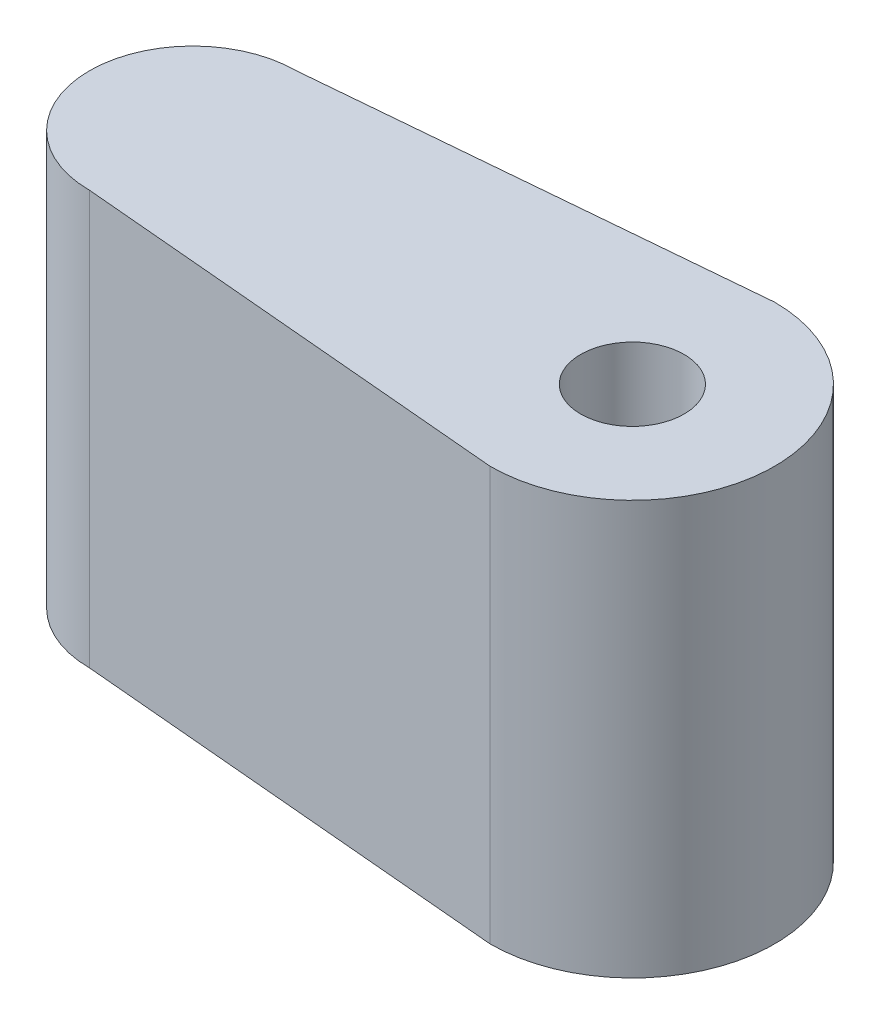
SolidWorks part; units mm, degrees
ref_plane "Front Plane" through (0, 0, 0) normal (0, 0, 1) x (1, 0, 0)
ref_plane "Top Plane" through (0, 0, 0) normal (0, 1, 0) x (1, 0, 0)
ref_plane "Right Plane" through (0, 0, 0) normal (1, 0, 0) x (0, 0, -1)
sketch "Sketch1" plane through (0, 0, 0) normal (0, 1, 0) x (1, 0, 0)
  line L0 (0, 0) -> (-8.5, 0) construction
  line L1 (-8.5, 2) -> (0, 2.75)
  line L2 (-8.5, -2) -> (0, -2.75)
  circle A0 centre (0, 0) radius 1
  arc A1 (-0.4815, -2.7075) -> (-0.4815, 2.7075) centre (0, 0) ccw
  arc A2 (-8.5, 2) -> (-8.5, -2) centre (-8.5, 0) ccw
  dimension "D1" = 2
  dimension "D2" = 5.5
  dimension "D3" = 4
  dimension "D4" = 8.5
extrude "Boss-Extrude1" add sketch "Sketch1" along normal blind 8
ref_plane "Plane1" through (-10.5, 0, 0) normal (-1, 0, 0) x (0, 0, 1)
sketch "Sketch2" plane through (-10.5, 0, 0) normal (-1, 0, 0) x (0, 0, 1)
  line L0 (0, 0) -> (0, 8) construction
  line L1 (2, 8) -> (-2, 8) construction
  line L2 (2, 8) -> (-2, 8) construction
  line L3 (-2, 0) -> (2, 0) construction
  line L4 (-2, 0) -> (2, 0) construction
  circle A0 centre (0, 4) radius 1
  dimension "D1" = 2
extrude "Cut-Extrude1" cut sketch "Sketch2" against normal blind 8
